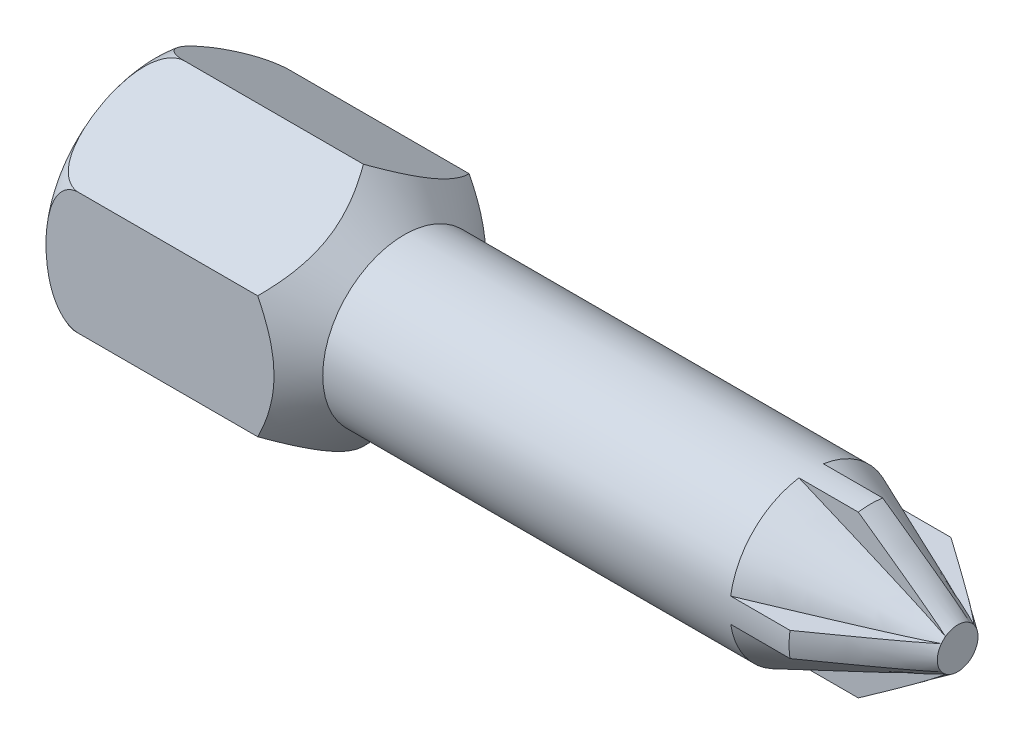
SolidWorks part; units mm, degrees
material "AISI 1020"
ref_plane "Front Plane" through (0, 0, 0) normal (0, 0, 1) x (1, 0, 0)
ref_plane "Top Plane" through (0, 0, 0) normal (0, 1, 0) x (1, 0, 0)
ref_plane "Right Plane" through (0, 0, 0) normal (1, 0, 0) x (0, 0, -1)
sketch "Sketch1" plane through (0, 0, 0) normal (0, 0, -1) x (1, 0, 0)
  line L0 (-28.1366, 0) -> (115.528, 0) construction
  line L1 (0, 0) -> (0, 10)
  line L2 (5, 15) -> (27, 15)
  line L3 (32, 10) -> (82, 10)
  line L4 (27, 15) -> (32, 10)
  line L5 (0, 0) -> (100, 0)
  line L6 (100, 0) -> (100, 2.5)
  line L8 (82, 10) -> (100, 2.5)
  arc A2 (0, 10) -> (5, 15) centre (5, 10) cw
  point P13 (0, 15)
  dimension "D2" = 5
  dimension "D9" = 5
  dimension "D1" = 30
  dimension "D3" = 68
  dimension "D4" = 135
  dimension "D5" = 100
  dimension "D6" = 20
  dimension "D7" = 18
revolve "Revolve1" add sketch "Sketch1" angle 360 about L0
sketch "Sketch2" plane through (0, 0, 0) normal (-1, 0, 0) x (0, 0, 1)
  line L7 (12.9904, -7.5) -> (12.9904, 7.5)
  line L8 (12.9904, 7.5) -> (0, 15)
  line L9 (0, 15) -> (-12.9904, 7.5)
  line L10 (-12.9904, 7.5) -> (-12.9904, -7.5)
  line L11 (-12.9904, -7.5) -> (0, -15)
  line L12 (0, -15) -> (12.9904, -7.5)
  circle A0 centre (0, 0) radius 15 construction
  circle A1 centre (0, 0) radius 15 construction
extrude "Cut-Extrude2" cut sketch "Sketch2" against normal up to next (100 mm away) flip side to cut
sketch "Sketch5" plane through (100, 0, 0) normal (1, 0, 0) x (0, 0, -1)
  line L0 (0, 0) -> (0, 4.6241) construction
  line L2 (-1.5, 2) -> (-1.5, 9.8869)
  line L4 (1.5, 2) -> (1.5, 9.8869)
  line L6 (-2, -1.5) -> (-9.8869, -1.5)
  line L7 (-2, 1.5) -> (-9.8869, 1.5)
  line L10 (-1.5, -2) -> (-1.5, -9.8869)
  line L12 (2, 1.5) -> (9.8869, 1.5)
  line L13 (2, -1.5) -> (9.8869, -1.5)
  line L14 (1.5, -2) -> (1.5, -9.8869)
  line L15 (1.5, 1.587) -> (1.5, 0.087) [skipped]
  circle A1 centre (0, 0) radius 10 construction
  arc A2 (1.5, 9.8869) -> (-1.5, 9.8869) centre (0, 0) ccw
  arc A3 (-9.8869, 1.5) -> (-9.8869, -1.5) centre (0, 0) ccw
  arc A4 (-1.5, -9.8869) -> (1.5, -9.8869) centre (0, 0) ccw
  arc A5 (9.8869, -1.5) -> (9.8869, 1.5) centre (0, 0) ccw
  arc A6 (-2, -1.5) -> (-1.5, -2) centre (0, 0) ccw
  arc A8 (-1.5, 2) -> (-2, 1.5) centre (0, 0) ccw
  arc A9 (2, 1.5) -> (1.5, 2) centre (0, 0) ccw
  arc A10 (1.5, -2) -> (2, -1.5) centre (0, 0) ccw
  circle A12 centre (0, 0) radius 2.5 construction
  point P26 (0, 0)
  dimension "D1" = 3
  dimension "D2" = 4
extrude "Boss-Extrude1" add sketch "Sketch5" against normal blind 18
sketch "Sketch6" plane through (0, 0, 0) normal (0, 0, 1) x (1, 0, 0)
  line L5 (100, 0) -> (107.8771, 0) construction
  line L6 (100, -1.5) -> (100, 1.5) construction
  line L7 (100, 2.5) -> (100, 10)
  line L8 (100, 9.8869) -> (100, 2) construction
  line L9 (100, 10) -> (89.2889, 10)
  line L10 (89.2889, 10) -> (100, 2.5)
  line L11 (100, 10) -> (32, 10) construction
  dimension "D1" = 35
  dimension "D2" = 5
revolve "Cut-Revolve1" cut sketch "Sketch6" angle 360 about L5
